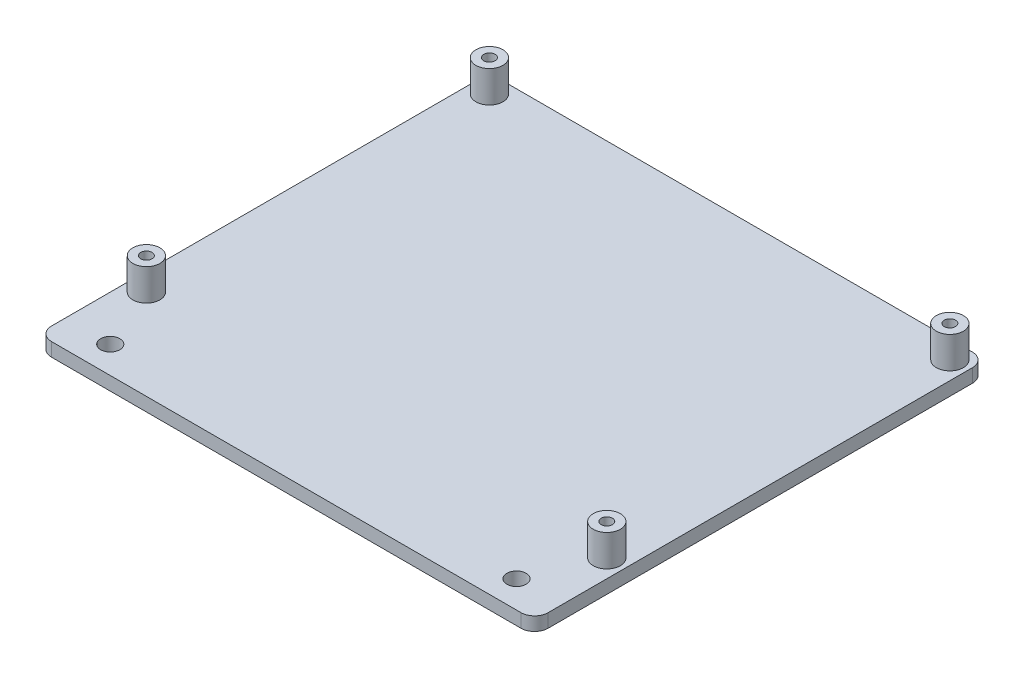
SolidWorks part; units mm, degrees
ref_plane "Front Plane" through (0, 0, 0) normal (0, 0, 1) x (1, 0, 0)
ref_plane "Top Plane" through (0, 0, 0) normal (0, 1, 0) x (1, 0, 0)
ref_plane "Right Plane" through (0, 0, 0) normal (1, 0, 0) x (0, 0, -1)
sketch "Sketch1" plane through (0, 0, 0) normal (0, 1, 0) x (1, 0, 0)
  line L0 (0, 16) -> (110, 16) construction
  line L1 (0, 0) -> (110, 0)
  line L3 (0, 100) -> (110, 100)
  line L5 (0, 100) -> (0, 16)
  line L6 (0, 0) -> (0, 16)
  line L7 (110, 100) -> (110, 16)
  line L8 (110, 0) -> (110, 16)
  line L9 (0, 58) -> (110, 58) construction
  line L10 (55, 100) -> (55, 0) construction
  line L11 (4, 58) -> (4, 96) construction
  line L12 (4, 96) -> (55, 96) construction
  line L13 (55, 96) -> (106, 96) construction
  line L14 (106, 96) -> (106, 58) construction
  line L15 (106, 58) -> (106, 20) construction
  line L16 (106, 20) -> (55, 20) construction
  line L17 (55, 20) -> (4, 20) construction
  line L18 (4, 20) -> (4, 58) construction
  circle A0 centre (4, 96) radius 1.25
  circle A1 centre (106, 96) radius 1.25
  circle A2 centre (106, 20) radius 1.25
  circle A3 centre (4, 20) radius 1.25
  dimension "D6" = 2.5
  dimension "D1" = 110
  dimension "D2" = 100
  dimension "D3" = 84
  dimension "D4" = 102
  dimension "D5" = 76
extrude "Boss-Extrude1" add sketch "Sketch1" along normal blind 3
fillet "Fillet1" radius 3 4 edges at (0, 1.5, -100) (110, 1.5, -100) (0, 1.5, 0) (110, 1.5, 0)
sketch "Sketch2" plane through (0, 3, 0) normal (0, 1, 0) x (1, 0, 0)
  circle A0 centre (4, 96) radius 1.25
  circle A1 centre (4, 96) radius 3
  circle A2 centre (106, 96) radius 1.25
  circle A3 centre (106, 96) radius 3
  circle A4 centre (106, 20) radius 1.25
  circle A5 centre (106, 20) radius 3
  circle A6 centre (4, 20) radius 1.25
  circle A7 centre (4, 20) radius 3
  circle A8 centre (4, 20) radius 1.25 construction
  circle A9 centre (4, 96) radius 1.25 construction
  circle A10 centre (106, 96) radius 1.25 construction
  circle A11 centre (106, 20) radius 1.25 construction
  dimension "D1" = 6
extrude "Boss-Extrude2" add sketch "Sketch2" along normal blind 7
sketch "Sketch4" plane through (0, 0, 0) normal (0, -1, 0) x (1, 0, 0)
  line L0 (0, -6) -> (110, -6) construction
  line L1 (0, 0) -> (0, -16) construction
  line L2 (110, 0) -> (110, -16) construction
  line L3 (0, -16) -> (110, -16) construction
  circle A0 centre (10, -6) radius 2.125
  circle A1 centre (100, -6) radius 2.125
  dimension "D2" = 4.25
  dimension "D1" = 10
  dimension "D3" = 10
  dimension "D4" = 10
extrude "Cut-Extrude1" cut sketch "Sketch4" against normal through all
